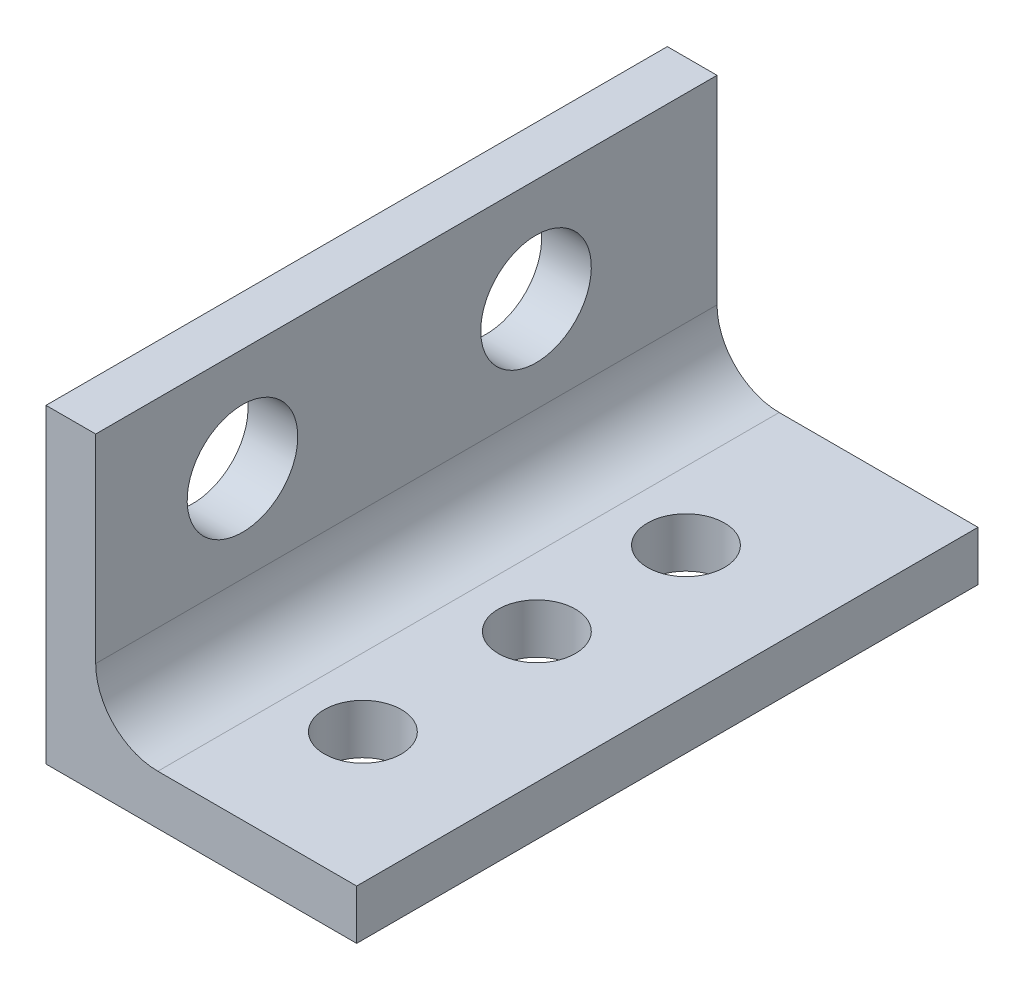
SolidWorks part; units mm, degrees
ref_plane "Front Plane" through (0, 0, 0) normal (0, 0, 1) x (1, 0, 0)
ref_plane "Top Plane" through (0, 0, 0) normal (0, 1, 0) x (1, 0, 0)
ref_plane "Right Plane" through (0, 0, 0) normal (1, 0, 0) x (0, 0, -1)
sketch "Sketch1" plane through (0, 0, 0) normal (0, 0, 1) x (1, 0, 0)
  line L0 (-6.35, 6.35) -> (-6.35, 0)
  line L1 (-6.35, 0) -> (0, 0)
  line L2 (-5.334, 6.35) -> (-5.334, 1.016)
  line L3 (-5.334, 1.016) -> (0, 1.016)
  line L4 (-5.334, 6.35) -> (-6.35, 6.35)
  line L5 (0, 1.016) -> (0, 0)
  dimension "D1" = 6.35
  dimension "D2" = 6.35
  dimension "D3" = 1.016
extrude "Boss-Extrude1" add sketch "Sketch1" along normal blind 12.7
sketch "Sketch3" plane through (0, 1.016, 0) normal (0, 1, 0) x (1, 0, 0)
  line L0 (-2.667, 0) -> (-2.667, -12.7) construction
  line L1 (0, 0) -> (-5.334, 0) construction
  line L3 (0, -12.7) -> (-5.334, -12.7) construction
  line L4 (0, -6.35) -> (-5.334, -6.35) construction
  line L5 (0, -12.7) -> (0, 0) construction
  line L6 (-5.334, -12.7) -> (-5.334, 0) construction
  circle A0 centre (-2.667, -9.906) radius 0.7874
  circle A1 centre (-2.667, -6.35) radius 0.7874
  circle A2 centre (-2.667, -3.302) radius 0.7874
  dimension "D1" = 1.5748
  dimension "D2" = 3.556
  dimension "D3" = 3.048
extrude "Cut-Extrude1" cut sketch "Sketch3" against normal blind 2.54
fillet "Fillet1" radius 1.27 1 edges at (-5.334, 1.016, 6.35)
sketch "Sketch4" plane through (-5.334, 0, 0) normal (1, 0, 0) x (0, 0, -1)
  line L0 (-12.7, 0) -> (0, 0) construction
  line L4 (-12.7, 2.286) -> (-12.7, 6.35) construction
  line L5 (-9.7, 4.24) -> (-0.6299, 4.24) construction
  circle A0 centre (-9.7, 4.24) radius 1.1303
  circle A1 centre (-3.7, 4.24) radius 1.1303
  dimension "D1" = 4.24
  dimension "D2" = 2.2606
  dimension "D4" = 6
  dimension "D3" = 3
extrude "Cut-Extrude2" cut sketch "Sketch4" against normal up to next
